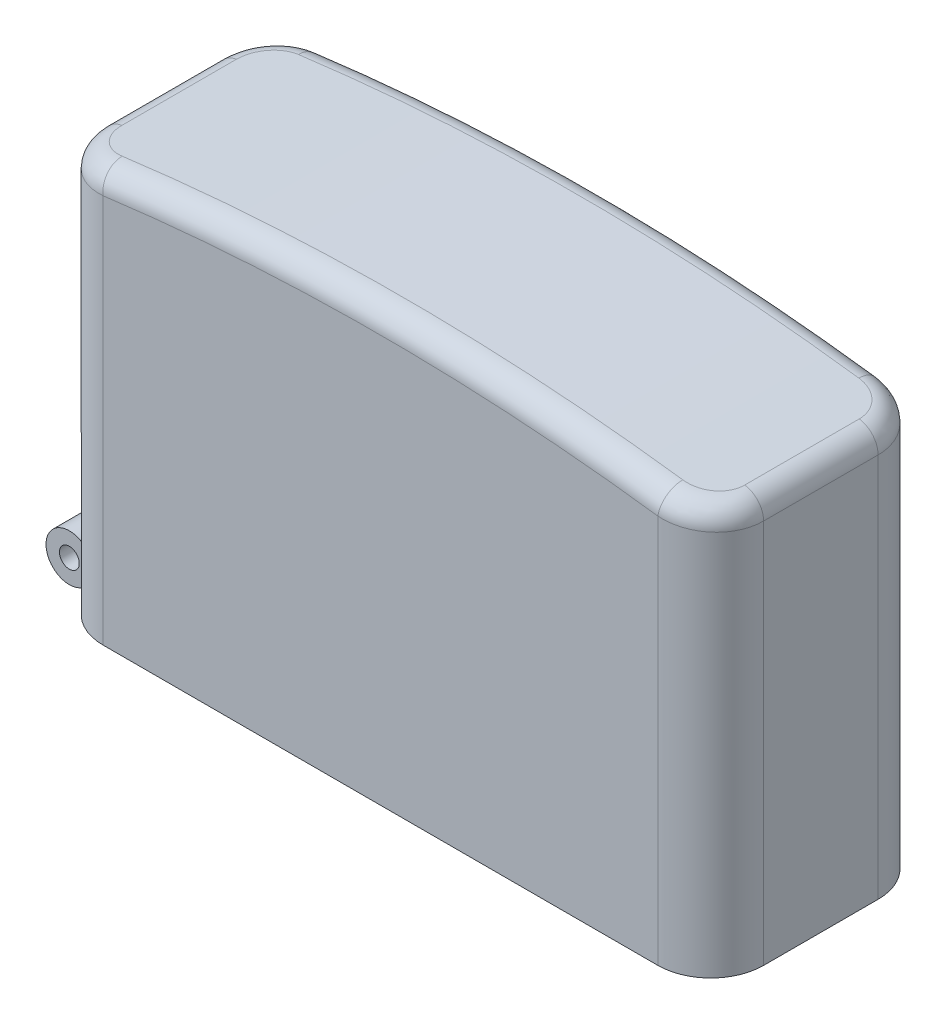
SolidWorks part; units mm, degrees
material "Chrome Stainless Steel"
ref_plane "Front Plane" through (0, 0, 0) normal (0, 0, 1) x (1, 0, 0)
ref_plane "Top Plane" through (0, 0, 0) normal (0, 1, 0) x (1, 0, 0)
ref_plane "Right Plane" through (0, 0, 0) normal (1, 0, 0) x (0, 0, -1)
sketch "Sketch1" plane through (0, 0, 0) normal (0, 0, 1) x (1, 0, 0)
  line L3 (0, 0) -> (38.1, 0)
  line L7 (0, 0) -> (0, 23.2918)
  line L8 (38.1, 0) -> (38.1, 23.2918)
  line L9 (19.05, 0) -> (19.05, 24.7583) construction
  arc A9 (0, 23.2918) -> (38.1, 23.2918) centre (19.05, -99.7017) cw
  dimension "D1" = 124.46
  dimension "D3" = 23.2918
  dimension "D7" = 38.1
extrude "Boss-Extrude1" add sketch "Sketch1" along normal blind 12.7
fillet "Fillet7" radius 3.048 4 edges at (38.1, 11.6459, 0) (38.1, 11.6459, 12.7) (0, 11.6459, 0) (0, 11.6459, 12.7)
fillet "Fillet8" radius 1.27 8 edges at (0, 23.2918, 6.35) (1.1304, 23.4616, 0.6788) (19.05, 24.7583, 0) (37.4449, 23.3915, 1.1601) (38.1, 23.2918, 6.35) (36.9696, 23.4616, 12.0212) (19.05, 24.7583, 12.7) (0.6551, 23.3915, 11.5399)
shell "Shell2" thickness 0.4572
sketch "Sketch2" plane through (0, 0, 0) normal (-1, 0, 0) x (0, 0, 1)
  line L0 (10.3251, 0) -> (2.3749, 0)
  line L5 (6.35, 22.1985) -> (6.35, 0) construction
  line L6 (9.652, 22.1985) -> (3.048, 22.1985) construction
  line L11 (0, 0) -> (3.048, 0) construction
  line L12 (2.3749, 0) -> (2.3749, 1.016)
  line L13 (2.3749, 1.016) -> (10.3251, 1.016)
  line L14 (10.3251, 0) -> (10.3251, 1.016)
  point P11 (6.35, 1.016)
  dimension "D1" = 7.9502
  dimension "D2" = 1.016
extrude "Cut-Extrude1" cut sketch "Sketch2" against normal blind 11.7856
sketch "Sketch4" plane through (0, 1.016, 0) normal (0, -1, 0) x (1, 0, 0)
  line L0 (0.0753, 7.1501) -> (-1.2709, 7.1501)
  line L1 (0.0753, 10.3251) -> (-1.2709, 10.3251)
  line L3 (0.0753, 8.7376) -> (-1.2709, 8.7376)
  line L5 (0.0753, 5.5626) -> (-1.2709, 5.5626)
  line L6 (-1.2709, 7.1501) -> (-1.2709, 5.5626)
  line L7 (0.0753, 3.9751) -> (-1.2709, 3.9751)
  line L8 (0.0753, 7.1501) -> (0.0753, 5.5626)
  line L9 (0.0753, 2.3876) -> (-1.2709, 2.3876)
  line L10 (-1.2709, 3.9751) -> (-1.2709, 2.3876)
  line L11 (0.0753, 3.9751) -> (0.0753, 2.3876)
  line L13 (-1.2709, 10.3251) -> (-1.2709, 8.7376)
  line L14 (0.0753, 10.3251) -> (0.0753, 8.7376)
  line L15 (-1.2709, 10.3251) -> (-1.2709, 2.3876) construction
  line L16 (-0.7014, 2.3876) -> (-0.7014, 12.6095) construction
  dimension "D1" = 1.5875
  dimension "D2" = 1.3462
revolve "Revolve1" add sketch "Sketch4" angle 360 about L15
sketch "Sketch5" plane through (0, 0, 2.3876) normal (0, 0, -1) x (-1, 0, 0)
  circle A0 centre (1.2709, 1.016) radius 0.5715
  arc A1 (-0.0753, 1.016) -> (-0.0724, 1.1035) centre (1.2709, 1.016) ccw construction
  dimension "D1" = 1.143
extrude "Cut-Extrude2" cut sketch "Sketch5" against normal through all
